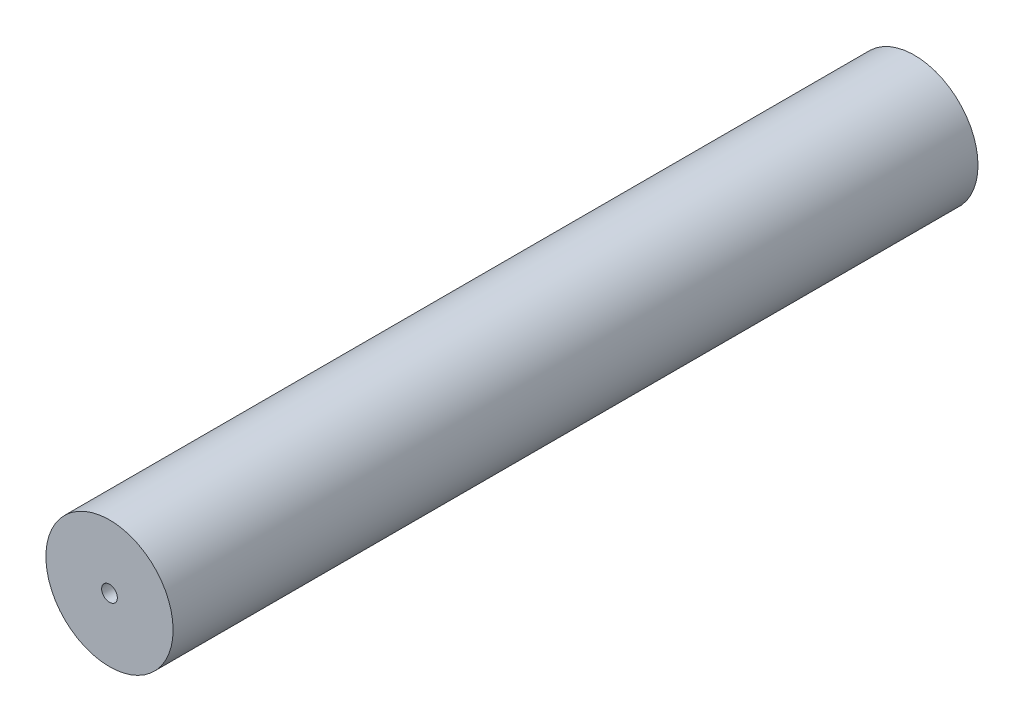
SolidWorks part; units mm, degrees
ref_plane "Front Plane" through (0, 0, 0) normal (0, 0, 1) x (1, 0, 0)
ref_plane "Top Plane" through (0, 0, 0) normal (0, 1, 0) x (1, 0, 0)
ref_plane "Right Plane" through (0, 0, 0) normal (1, 0, 0) x (0, 0, -1)
sketch "Sketch1" plane through (0, 0, 0) normal (0, 0, 1) x (1, 0, 0)
  circle A0 centre (0, 0) radius 3.161
  dimension "D1" = 6.3221
extrude "Boss-Extrude1" add sketch "Sketch1" along normal blind 40
sketch "Sketch2" plane through (0, 0, 40) normal (0, 0, 1) x (1, 0, 0)
  circle A0 centre (0, 0) radius 0.39
  dimension "D1" = 0.78
extrude "Cut-Extrude1" cut sketch "Sketch2" against normal up to next
